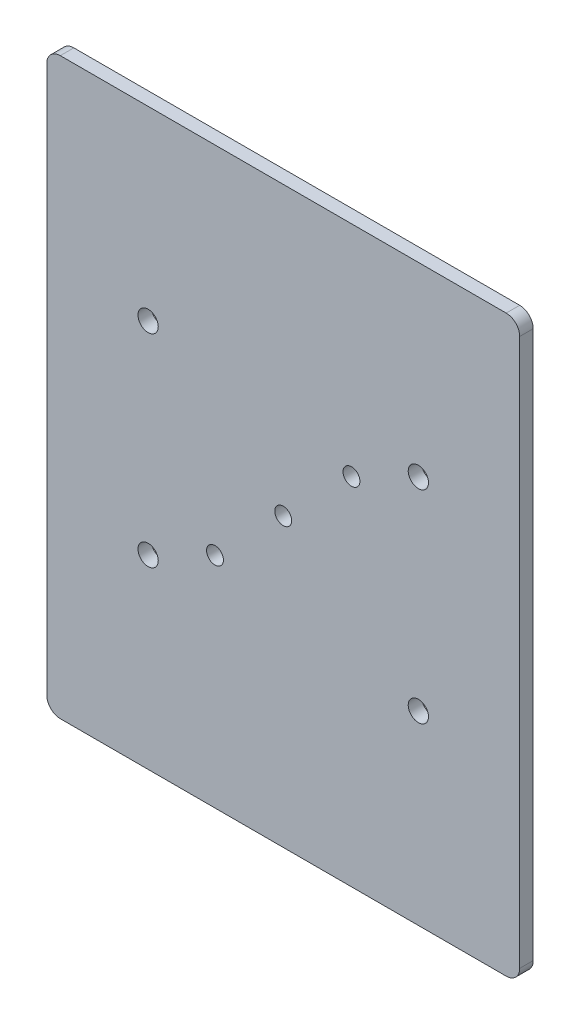
SolidWorks part; units mm, degrees
material "环氧板3240"
ref_plane "前视基准面" through (0, 0, 0) normal (0, 0, 1) x (1, 0, 0)
ref_plane "上视基准面" through (0, 0, 0) normal (0, 1, 0) x (1, 0, 0)
ref_plane "右视基准面" through (0, 0, 0) normal (1, 0, 0) x (0, 0, -1)
other "Configuration Table"
sketch "草图1" plane through (0, 0, 0) normal (0, 0, 1) x (1, 0, 0)
  line L0 (-35, 0) -> (35, 0) construction
  line L1 (-35, 42.5) -> (35, 42.5)
  line L2 (-35, 42.5) -> (-35, -42.5)
  line L3 (-35, -42.5) -> (35, -42.5)
  line L4 (35, 42.5) -> (35, -42.5)
  line L5 (0, 42.5) -> (0, -42.5) construction
  line L6 (-10.1, 10.1) -> (-10.1, -10.1) construction
  line L7 (20, -15) -> (-20, -15) construction
  line L8 (20, -15) -> (20, 15) construction
  line L9 (20, 15) -> (-20, 15) construction
  line L10 (-20, -15) -> (-20, 15) construction
  line L11 (20, -15) -> (-20, 15) construction
  line L12 (20, 15) -> (-20, -15) construction
  line L13 (-10.1, -10.1) -> (10.1, -10.1) construction
  line L14 (10.1, -10.1) -> (10.1, 10.1) construction
  line L15 (10.1, 10.1) -> (-10.1, 10.1) construction
  circle A0 centre (-20, 15) radius 1.5
  circle A1 centre (20, 15) radius 1.5
  circle A2 centre (-20, -15) radius 1.5
  circle A3 centre (20, -15) radius 1.5
  circle A4 centre (-10.1, 10.1) radius 1.25 construction
  circle A5 centre (10.1, -10.1) radius 1.25 construction
  circle A6 centre (10.1, 10.1) radius 1.25
  circle A7 centre (-10.1, -10.1) radius 1.25
  circle A8 centre (0, 0) radius 1.25
  point P0 (121.177, 27.7487)
  point P9 (0, 0)
  dimension "D5" = 3
  dimension "D6" = 20.2
  dimension "D8" = 2.5
  dimension "D1" = 85
  dimension "D2" = 70
  dimension "D3" = 40
  dimension "D4" = 30
  dimension "D7" = 20.2
extrude "凸台-拉伸1" add sketch "草图1" along normal blind 2
fillet "圆角1" radius 2 4 edges at (35, -42.5, 1) (-35, -42.5, 1) (35, 42.5, 1) (-35, 42.5, 1)
